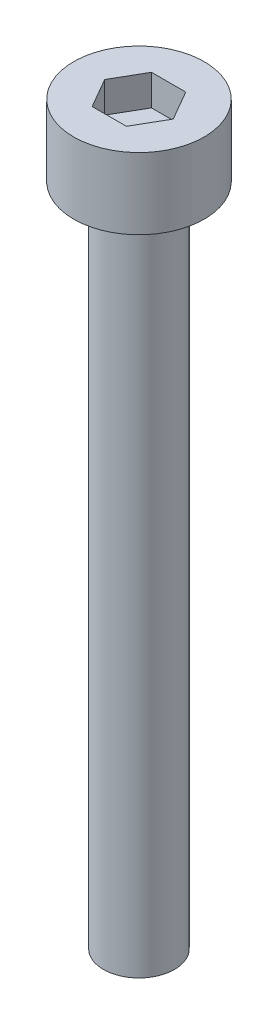
SolidWorks part; units mm, degrees
material "AISI 304"
ref_plane "前视基准面" through (0, 0, 0) normal (0, 0, 1) x (1, 0, 0)
ref_plane "上视基准面" through (0, 0, 0) normal (0, 1, 0) x (1, 0, 0)
ref_plane "右视基准面" through (0, 0, 0) normal (1, 0, 0) x (0, 0, -1)
sketch "草图1" plane through (0, 0, 0) normal (0, 1, 0) x (1, 0, 0)
  circle A0 centre (0, 0) radius 2.75
  dimension "D1" = 5.5
extrude "杯头" add sketch "草图1" along normal blind 3
sketch "草图2" plane through (0, 3, 0) normal (0, 1, 0) x (1, 0, 0)
  line L1 (1.4434, 0) -> (0.7217, 1.25)
  line L2 (0.7217, 1.25) -> (-0.7217, 1.25)
  line L3 (-0.7217, 1.25) -> (-1.4434, 0)
  line L4 (-1.4434, 0) -> (-0.7217, -1.25)
  line L5 (-0.7217, -1.25) -> (0.7217, -1.25)
  line L6 (0.7217, -1.25) -> (1.4434, 0)
  circle A0 centre (0, 0) radius 1.25 construction
  dimension "D1" = 2.5
extrude "内六角口" cut sketch "草图2" against normal blind 1.3
sketch "草图3" plane through (0, 0, 0) normal (0, -1, 0) x (1, 0, 0)
  circle A0 centre (0, 0) radius 1.5
  dimension "D1" = 3
extrude "螺纹长" add sketch "草图3" along normal blind 28
